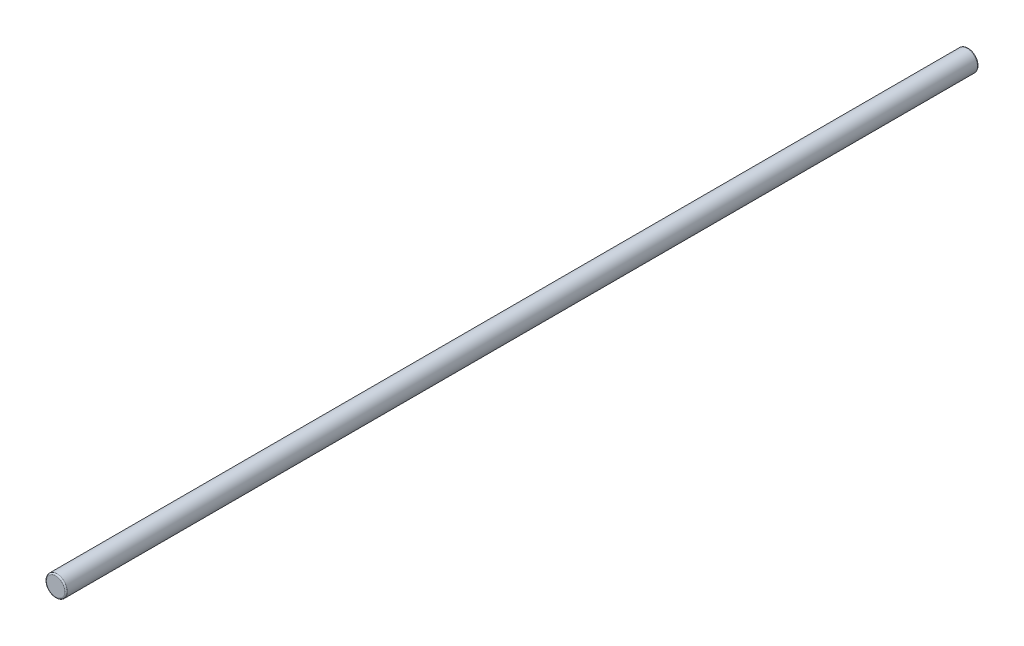
SolidWorks part; units mm, degrees
ref_plane "Plan de face" through (0, 0, 0) normal (0, 0, 1) x (1, 0, 0)
ref_plane "Plan de dessus" through (0, 0, 0) normal (0, 1, 0) x (1, 0, 0)
ref_plane "Plan de droite" through (0, 0, 0) normal (1, 0, 0) x (0, 0, -1)
sketch "Esquisse1" plane through (0, 0, 0) normal (0, 0, 1) x (1, 0, 0)
  circle A0 centre (0, 0) radius 4
extrude "Boss.-Extru.1" add sketch "Esquisse1" along normal blind 350
fillet "Congé1" radius 0.5 2 edges at (4, 0, 350) (4, 0, 0)
